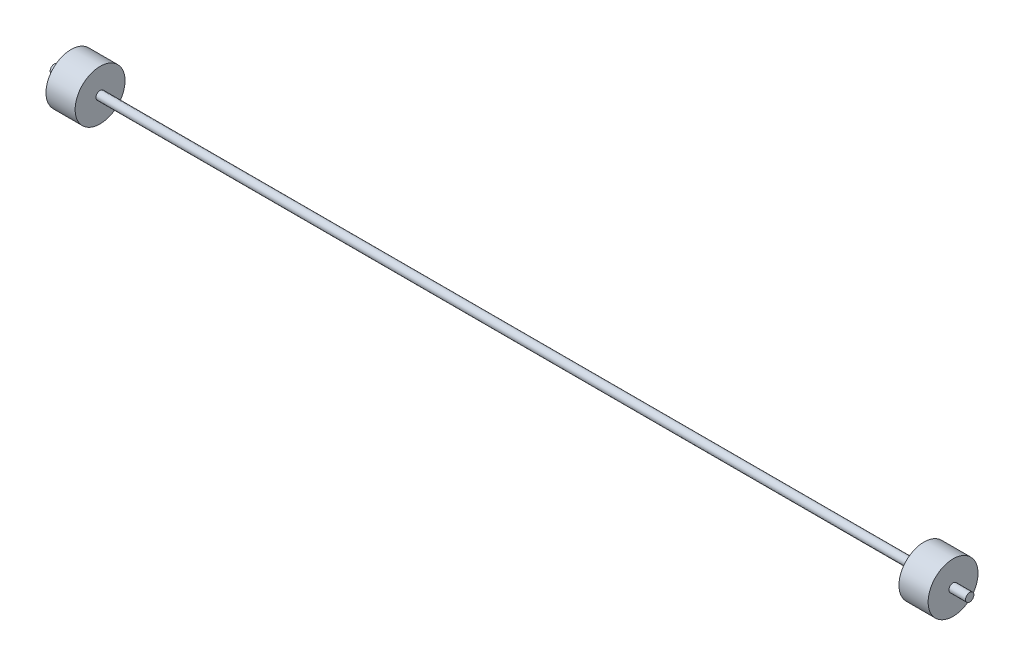
SolidWorks part; units mm, degrees
material "AISI 316 Annealed Stainless Steel Bar (SS)"
ref_plane "Front Plane" through (0, 0, 0) normal (0, 0, 1) x (1, 0, 0)
ref_plane "Top Plane" through (0, 0, 0) normal (0, 1, 0) x (1, 0, 0)
ref_plane "Right Plane" through (0, 0, 0) normal (1, 0, 0) x (0, 0, -1)
sketch "Sketch1" plane through (0, 0, 0) normal (0, 0, 1) x (1, 0, 0)
  line L0 (-388.8887, 0) -> (529.3207, 0) construction
  line L1 (-396.6611, 76.2) -> (-396.6611, 12.7)
  line L2 (-396.6611, 76.2) -> (-307.7611, 76.2)
  line L3 (-307.7611, 76.2) -> (-307.7611, 12.7)
  line L4 (-307.7611, 12.7) -> (2206.8389, 12.7)
  line L5 (2206.8389, 12.7) -> (2206.8389, 76.2)
  line L6 (2206.8389, 76.2) -> (2295.7389, 76.2)
  line L7 (-447.4611, 0) -> (2346.5389, 0)
  line L8 (-396.6611, 12.7) -> (-447.4611, 12.7)
  line L9 (-447.4611, 12.7) -> (-447.4611, 0)
  line L11 (2295.7389, 76.2) -> (2295.7389, 12.7)
  line L12 (2295.7389, 12.7) -> (2346.5389, 12.7)
  line L13 (2346.5389, 12.7) -> (2346.5389, 0)
  point P11 (2346.5389, 6.35)
  dimension "D1" = 76.2
  dimension "D2" = 12.7
  dimension "D3" = 12.7
  dimension "D4" = 12.7
  dimension "D5" = 12.7
  dimension "D6" = 76.2
  dimension "D7" = 50.8
  dimension "D8" = 2692.4
  dimension "D9" = 88.9
  dimension "D10" = 88.9
  dimension "D11" = 2794
revolve "Revolve2" add sketch "Sketch1" angle 360 about L0
